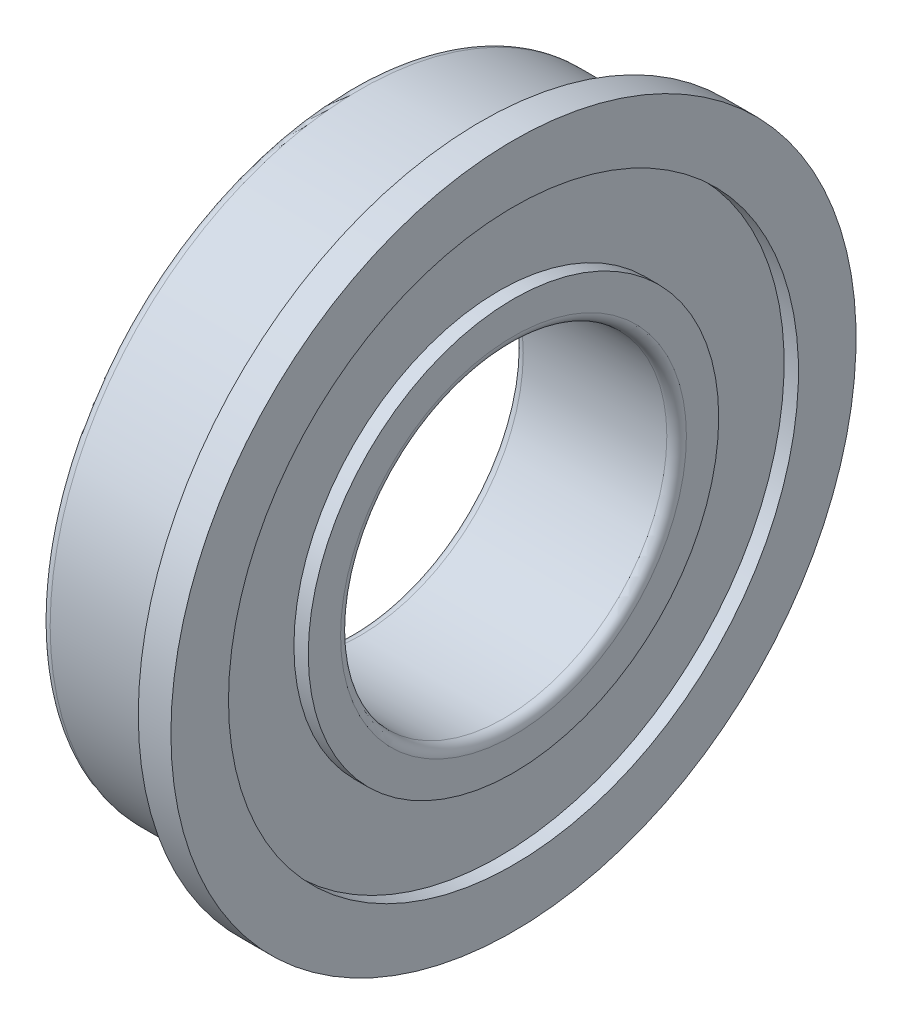
SolidWorks part; units mm, degrees
ref_plane "Front Plane" through (0, 0, 0) normal (0, 0, 1) x (1, 0, 0)
ref_plane "Top Plane" through (0, 0, 0) normal (0, 1, 0) x (1, 0, 0)
ref_plane "Right Plane" through (0, 0, 0) normal (1, 0, 0) x (0, 0, -1)
sketch "Sketch1" plane through (0, 0, 0) normal (0, 0, 1) x (1, 0, 0)
  line L0 (-4, 0) -> (1, 0) construction
  line L1 (0, 9.7) -> (0, 10.5)
  line L2 (0, 10.5) -> (1, 10.5)
  line L3 (1, 10.5) -> (1, 8.735)
  line L4 (1, 5) -> (-4, 5)
  line L5 (-4, 5) -> (-4, 6.29)
  line L6 (-4, 9.5) -> (-0.2, 9.5)
  line L7 (-4, 8.735) -> (-3.56, 8.735)
  line L8 (-3.56, 8.735) -> (-3.56, 6.29)
  line L9 (-3.56, 6.29) -> (-4, 6.29)
  line L10 (1, 8.735) -> (0.56, 8.735)
  line L11 (0.56, 8.735) -> (0.56, 6.29)
  line L12 (0.56, 6.29) -> (1, 6.29)
  line L13 (-4, 8.735) -> (-4, 9.5)
  line L14 (1, 6.29) -> (1, 5)
  arc A0 (-0.2, 9.5) -> (0, 9.7) centre (0, 9.5) ccw
  dimension "FIX_1" = 0.2
  dimension "D_s" = 10
  dimension "C" = 1
  dimension "MSM_2" = 12.58
  dimension "MSM_1" = 17.47
  dimension "D" = 19
  dimension "D1." = 21
  dimension "B" = 5
  dimension "MSM_3" = 0.44
revolve "Revolve1" add sketch "Sketch1" angle 360 about L0
fillet "Fillet1" radius 0.3 3 edges at (1, 0, 5) (-4, 0, 5) (-4, 0, 9.5)
